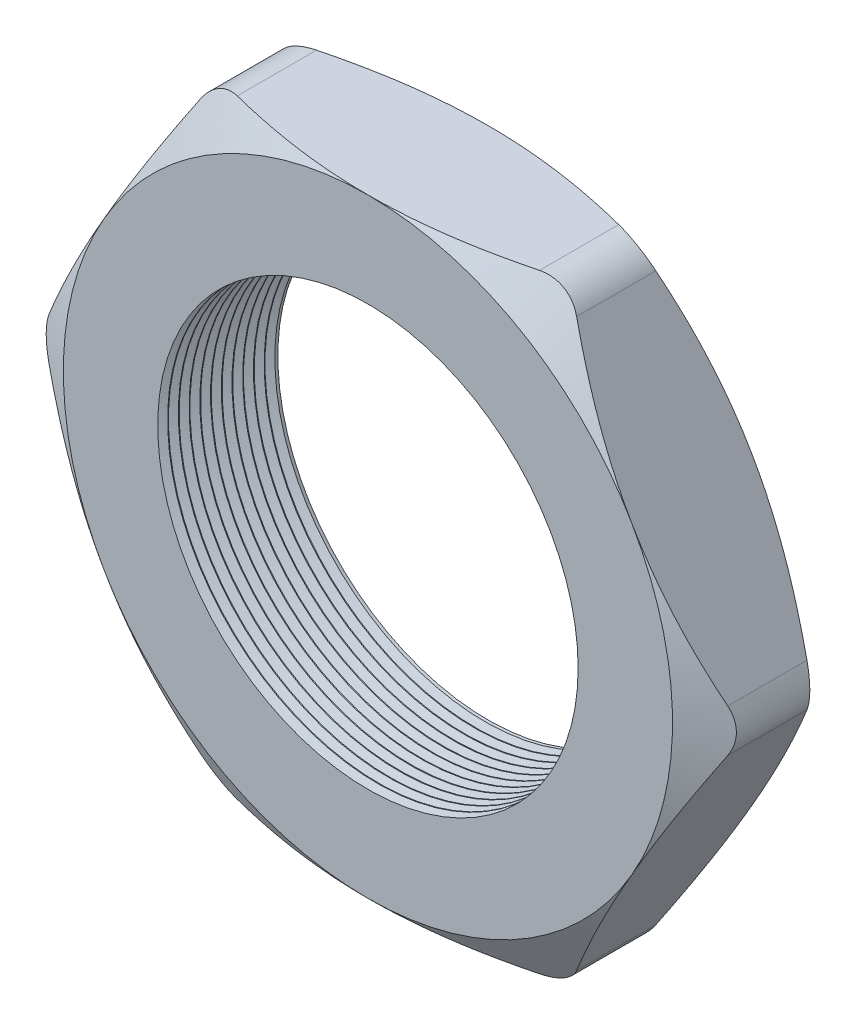
SolidWorks part; units mm, degrees
ref_plane "Front Plane" through (0, 0, 0) normal (0, 0, 1) x (1, 0, 0)
ref_plane "Top Plane" through (0, 0, 0) normal (0, 1, 0) x (1, 0, 0)
ref_plane "Right Plane" through (0, 0, 0) normal (1, 0, 0) x (0, 0, -1)
sketch "Sketch1" plane through (0, 0, 0) normal (0, 0, 1) x (1, 0, 0)
  line L1 (-20.8239, 0) -> (-10.4119, -18.034)
  line L2 (-10.4119, -18.034) -> (10.4119, -18.034)
  line L3 (10.4119, -18.034) -> (20.8239, 0)
  line L4 (20.8239, 0) -> (10.4119, 18.034)
  line L5 (10.4119, 18.034) -> (-10.4119, 18.034)
  line L6 (-10.4119, 18.034) -> (-20.8239, 0)
  circle A0 centre (0, 0) radius 18.034 construction
  circle A1 centre (0, 0) radius 12.446
  dimension "TS" = 24.892
  dimension "H" = 36.068
extrude "Extrude1" add sketch "Sketch1" along normal blind 7.112
sketch "Sketch2" plane through (0, 0, 7.112) normal (0, 0, 1) x (1, 0, 0)
  line L0 (10.4119, 18.034) -> (-10.4119, 18.034) construction
  circle A0 centre (0, 0) radius 18.034
extrude "Cut-Extrude1" cut sketch "Sketch2" against normal through all draft 60 flip side to cut
sketch "Sketch3" plane through (0, 0, 0) normal (0, 0, -1) x (-1, 0, 0)
  line L0 (-10.4119, 18.034) -> (10.4119, 18.034) construction
  circle A0 centre (0, 0) radius 18.034
extrude "Cut-Extrude2" cut sketch "Sketch3" against normal through all draft 60 flip side to cut
fillet "Fillet1" radius 2.54 6 edges at (20.8239, 0, 3.556) (10.4119, -18.034, 3.556) (-10.4119, -18.034, 3.556) (-20.8239, 0, 3.556) (-10.4119, 18.034, 3.556) (10.4119, 18.034, 3.556)
sketch "Sketch4" plane through (0, 0, 0) normal (0, 1, 0) x (1, 0, 0)
  line L0 (-12.446, -7.112) -> (-12.446, -6.5254)
  line L1 (-12.446, 0) -> (-12.446, -7.112) construction
  line L2 (-12.446, -6.5254) -> (-12.954, -6.8187)
  line L3 (-12.954, -6.8187) -> (-12.446, -7.112)
  dimension "D1" = 60
  dimension "D2" = 60
  dimension "D3" = 0.508
revolve "Cut-Revolve1" cut sketch "Sketch4" angle 360 about axis through (0, 0, 0) along (0, 0, 1)
pattern_linear "LPattern1" count 11 spacing 0.635 along (0, 0, -1) of "Cut-Revolve1"
